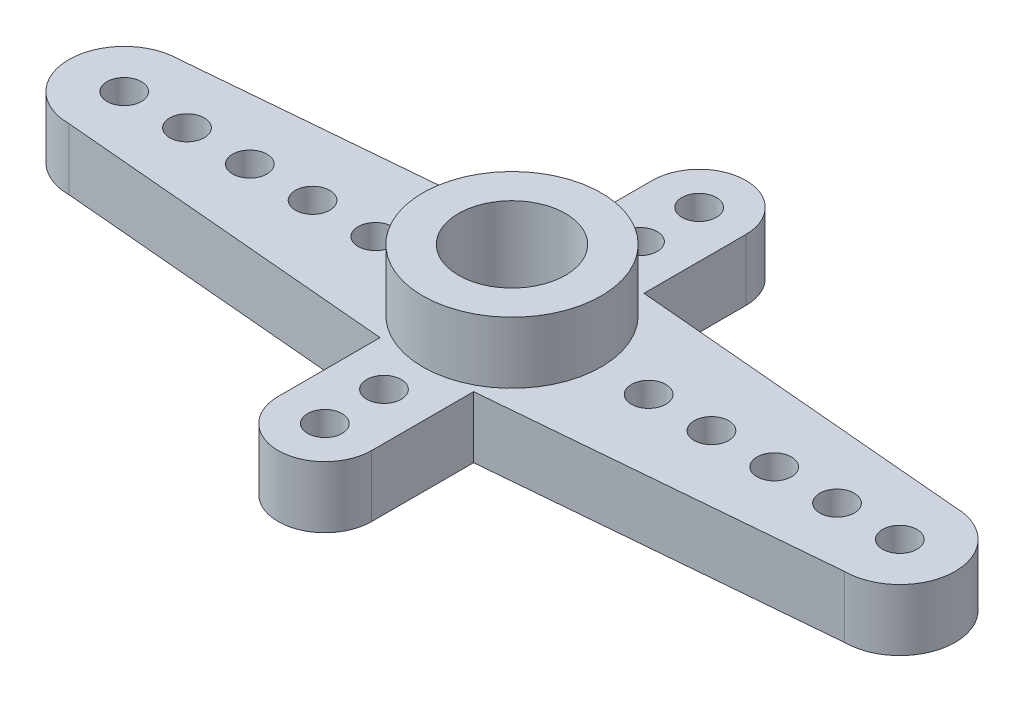
SolidWorks part; units mm, degrees
ref_plane "Front Plane" through (0, 0, 0) normal (0, 0, 1) x (1, 0, 0)
ref_plane "Top Plane" through (0, 0, 0) normal (0, 1, 0) x (1, 0, 0)
ref_plane "Right Plane" through (0, 0, 0) normal (1, 0, 0) x (0, 0, -1)
sketch "Sketch1" plane through (0, 0, 0) normal (0, 1, 0) x (1, 0, 0)
  line L1 (18, 0) -> (18, 3.625) construction
  line L2 (18, 0) -> (18, -3.625) construction
  line L12 (2.25, -2.25) -> (16.1, -3.4591)
  line L13 (2.25, 2.25) -> (16.1, 3.4591)
  line L15 (18, 0) -> (21.625, 0) construction
  line L16 (18, 0) -> (21.625, 0) construction
  line L18 (0, 0) -> (1.55, 0) construction
  line L19 (1.55, 0) -> (2.25, 0) construction
  line L20 (33.75, -2.25) -> (19.9, -3.4591)
  line L21 (16.1, 7.6) -> (16.1, 3.4591)
  line L22 (19.9, 7.6) -> (19.9, 3.4591)
  line L23 (33.75, 2.25) -> (19.9, 3.4591)
  line L24 (18, 9.5) -> (18, 8.3) construction
  line L25 (18, 8.3) -> (18, 7.6) construction
  line L26 (18, 8.3) -> (18, 4.5) construction
  line L27 (18, 4.5) -> (18, 5.2) construction
  line L28 (16.1, -7.6) -> (16.1, -3.4591)
  line L29 (19.9, -7.6) -> (19.9, -3.4591)
  circle A0 centre (18, 0) radius 2.175
  circle A1 centre (18, 0) radius 3.625
  circle A4 centre (18, 0) radius 1.25
  arc A7 (2.25, 2.25) -> (2.25, -2.25) centre (2.25, 0) ccw
  circle A8 centre (2.25, 0) radius 0.7
  circle A9 centre (4.8, 0) radius 0.7
  circle A11 centre (7.35, 0) radius 0.7
  circle A12 centre (9.9, 0) radius 0.7
  circle A13 centre (12.45, 0) radius 0.7
  arc A15 (19.9, 7.6) -> (16.1, 7.6) centre (18, 7.6) ccw
  circle A16 centre (23.55, 0) radius 0.7
  circle A17 centre (26.1, 0) radius 0.7
  circle A18 centre (28.65, 0) radius 0.7
  circle A19 centre (31.2, 0) radius 0.7
  circle A20 centre (33.75, 0) radius 0.7
  arc A21 (33.75, 2.25) -> (33.75, -2.25) centre (33.75, 0) cw
  circle A22 centre (18, 7.6) radius 0.7
  circle A23 centre (18, 5.2) radius 0.7
  circle A24 centre (18, -5.2) radius 0.7
  circle A25 centre (18, -7.6) radius 0.7
  arc A26 (19.9, -7.6) -> (16.1, -7.6) centre (18, -7.6) cw
  dimension "D1" = 2.55
  dimension "D2" = 2.55
  dimension "D3" = 2.55
  dimension "D4" = 2.55
  dimension "D5" = 1.4
sketch "Sketch6" plane through (0, 0, 0) normal (0, 1, 0) x (1, 0, 0)
  line L0 (16.1, 7.6) -> (16.1, 3.4591) construction
  line L1 (19.9, 7.6) -> (19.9, 3.4591) construction
  line L2 (33.75, 2.25) -> (19.9, 3.4591) construction
  line L3 (33.75, -2.25) -> (19.9, -3.4591) construction
  line L4 (19.9, -7.6) -> (19.9, -3.4591) construction
  line L5 (16.1, -7.6) -> (16.1, -3.4591) construction
  line L6 (2.25, -2.25) -> (16.1, -3.4591) construction
  line L7 (2.25, 2.25) -> (16.1, 3.4591) construction
  line L8 (16.1, 7.6) -> (16.1, 3.4591)
  line L9 (19.9, 7.6) -> (19.9, 3.4591)
  line L10 (33.75, 2.25) -> (19.9, 3.4591)
  line L11 (33.75, -2.25) -> (19.9, -3.4591)
  line L12 (19.9, -7.6) -> (19.9, -3.4591)
  line L13 (16.1, -7.6) -> (16.1, -3.4591)
  line L14 (2.25, -2.25) -> (16.1, -3.4591)
  line L15 (2.25, 2.25) -> (16.1, 3.4591)
  circle A0 centre (33.75, 0) radius 0.7 construction
  circle A1 centre (31.2, 0) radius 0.7 construction
  circle A2 centre (28.65, 0) radius 0.7 construction
  circle A3 centre (26.1, 0) radius 0.7 construction
  circle A4 centre (23.55, 0) radius 0.7 construction
  circle A5 centre (18, -7.6) radius 0.7 construction
  circle A6 centre (18, -5.2) radius 0.7 construction
  circle A7 centre (12.45, 0) radius 0.7 construction
  circle A8 centre (9.9, 0) radius 0.7 construction
  circle A9 centre (7.35, 0) radius 0.7 construction
  circle A10 centre (4.8, 0) radius 0.7 construction
  circle A11 centre (2.25, 0) radius 0.7 construction
  circle A12 centre (18, 5.2) radius 0.7 construction
  circle A13 centre (18, 7.6) radius 0.7 construction
  arc A14 (19.9, 7.6) -> (16.1, 7.6) centre (18, 7.6) ccw construction
  arc A15 (33.75, -2.25) -> (33.75, 2.25) centre (33.75, 0) ccw construction
  arc A16 (16.1, -7.6) -> (19.9, -7.6) centre (18, -7.6) ccw construction
  arc A17 (2.25, 2.25) -> (2.25, -2.25) centre (2.25, 0) ccw construction
  circle A18 centre (33.75, 0) radius 0.7
  circle A19 centre (31.2, 0) radius 0.7
  circle A20 centre (28.65, 0) radius 0.7
  circle A21 centre (26.1, 0) radius 0.7
  circle A22 centre (23.55, 0) radius 0.7
  circle A23 centre (18, -7.6) radius 0.7
  circle A24 centre (18, -5.2) radius 0.7
  circle A25 centre (12.45, 0) radius 0.7
  circle A26 centre (9.9, 0) radius 0.7
  circle A27 centre (7.35, 0) radius 0.7
  circle A28 centre (4.8, 0) radius 0.7
  circle A29 centre (2.25, 0) radius 0.7
  circle A30 centre (18, 5.2) radius 0.7
  circle A31 centre (18, 7.6) radius 0.7
  arc A32 (19.9, 7.6) -> (16.1, 7.6) centre (18, 7.6) ccw
  arc A33 (33.75, -2.25) -> (33.75, 2.25) centre (33.75, 0) ccw
  arc A34 (16.1, -7.6) -> (19.9, -7.6) centre (18, -7.6) ccw
  arc A35 (2.25, 2.25) -> (2.25, -2.25) centre (2.25, 0) ccw
extrude "Boss-Extrude3" add sketch "Sketch6" along normal blind 2.5
sketch "Sketch7" plane through (0, 2.5, 0) normal (0, 1, 0) x (1, 0, 0)
  circle A0 centre (18, 0) radius 3.625 construction
  circle A1 centre (18, 0) radius 3.625
  dimension "D1" = 7.25
extrude "Boss-Extrude4" add sketch "Sketch7" along normal blind 2.5
sketch "Sketch8" plane through (0, 5, 0) normal (0, 1, 0) x (1, 0, 0)
  circle A0 centre (18, 0) radius 2.175 construction
  circle A1 centre (18, 0) radius 2.175
extrude "Cut-Extrude3" cut sketch "Sketch8" against normal blind 3.4
sketch "Sketch9" plane through (0, 1.6, 0) normal (0, 1, 0) x (1, 0, 0)
  circle A0 centre (18, 0) radius 1.25 construction
  circle A1 centre (18, 0) radius 1.25
extrude "Cut-Extrude4" cut sketch "Sketch9" against normal up to next
